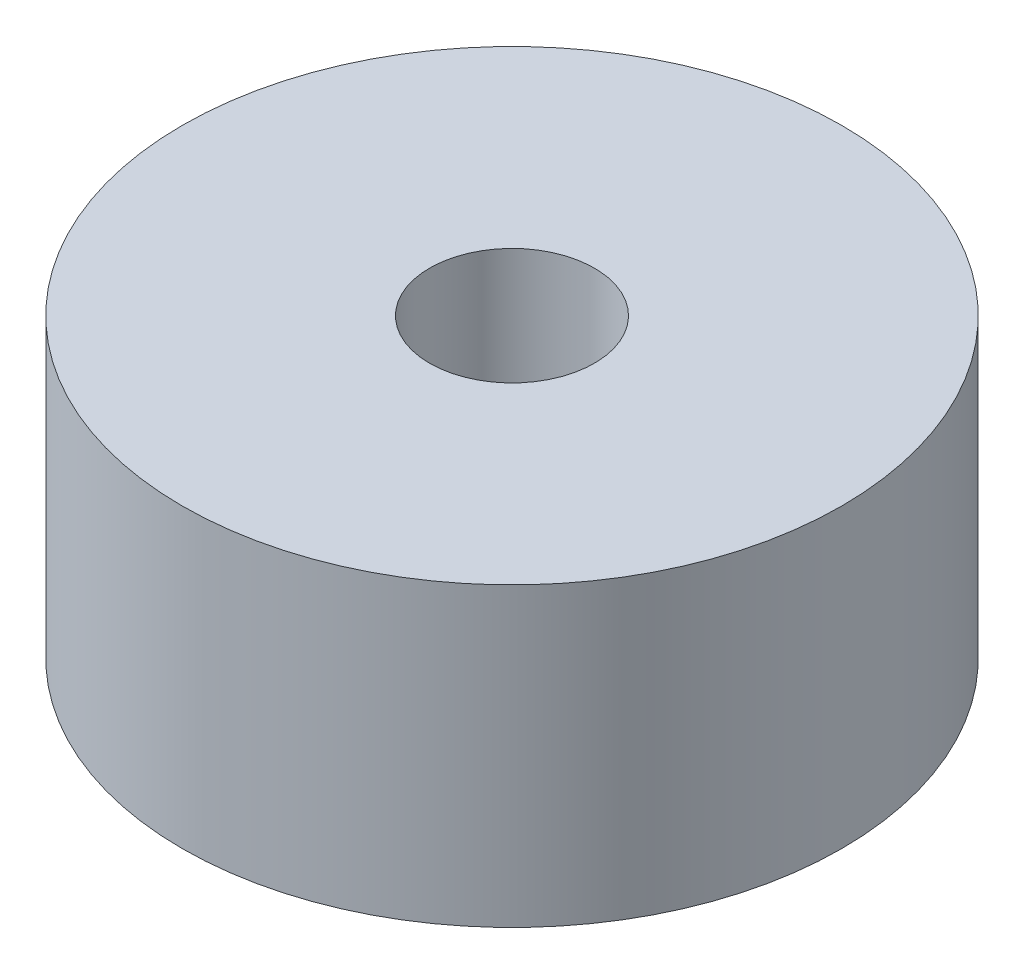
SolidWorks part; units mm, degrees
ref_plane "Front Plane" through (0, 0, 0) normal (0, 0, 1) x (1, 0, 0)
ref_plane "Top Plane" through (0, 0, 0) normal (0, 1, 0) x (1, 0, 0)
ref_plane "Right Plane" through (0, 0, 0) normal (1, 0, 0) x (0, 0, -1)
sketch "Sketch1" plane through (0, 0, 0) normal (0, 1, 0) x (1, 0, 0)
  circle A0 centre (0, 0) radius 20
  dimension "D1" = 40
extrude "Boss-Extrude1" add sketch "Sketch1" along normal blind 18
sketch "Sketch2" plane through (0, 18, 0) normal (0, 1, 0) x (1, 0, 0)
  circle A0 centre (0, 0) radius 5
  dimension "D1" = 10
extrude "Cut-Extrude1" cut sketch "Sketch2" against normal blind 10
sketch "Sketch3" plane through (0, 0, 0) normal (0, -1, 0) x (1, 0, 0)
  line L1 (11, -11) -> (-11, -11)
  line L2 (11, -11) -> (11, 11)
  line L3 (11, 11) -> (-11, 11)
  line L4 (-11, -11) -> (-11, 11)
  circle A0 centre (11, -11) radius 1.5
  circle A1 centre (-11, -11) radius 1.5
  circle A2 centre (11, 11) radius 1.5
  circle A3 centre (-11, 11) radius 1.5
  point P4 (0, -11)
  point P6 (-11, 0)
  dimension "D3" = 3
  dimension "D1" = 22
  dimension "D2" = 22
extrude "Cut-Extrude2" cut sketch "Sketch3" against normal blind 8 contours A0 | A1 | A2 | A3
